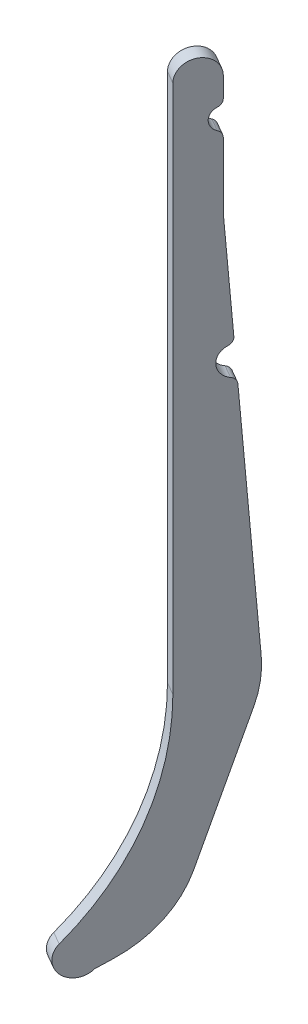
SolidWorks part; units mm, degrees
ref_plane "Front Plane" through (0, 0, 0) normal (0, 0, 1) x (1, 0, 0)
ref_plane "Top Plane" through (0, 0, 0) normal (0, 1, 0) x (1, 0, 0)
ref_plane "Right Plane" through (0, 0, 0) normal (1, 0, 0) x (0, 0, -1)
sketch "Sketch1" plane through (-22.6848, 0, -13.0971) normal (-0.866, 0, -0.5) x (-0.5, 0, 0.866)
  line L0 (-50.2251, -207.1163) -> (-50.2251, -63.6685) construction
  line L1 (-51.2251, -207.1163) -> (-51.2251, -63.6685)
  line L2 (25.7749, -207.1163) -> (-28.6723, -261.5635) construction
  line L3 (25.7749, -207.1163) -> (20.9854, -66.8615) construction
  line L4 (-61.2251, -96.0502) -> (-61.2251, -78.251)
  line L5 (-61.2251, -96.0502) -> (-63.3181, -125.3186)
  line L6 (-67.3143, -212.7397) -> (-55.3285, -249.1114)
  line L7 (-39.2993, -267.0104) -> (-35.7434, -268.6346)
  line L8 (-61.2251, -69.0859) -> (-61.2251, -63.6685)
  line L9 (-61.2251, -207.1163) -> (-61.2251, -63.6685) construction
  line L10 (-64.1251, -136.6035) -> (-68.7451, -201.2104)
  circle A0 centre (25.7749, -207.1163) radius 76 construction
  arc A1 (-50.2251, -207.1163) -> (25.7749, -283.1163) centre (25.7749, -207.1163) ccw construction
  arc A2 (-51.2251, -207.1163) -> (-28.6723, -261.5635) centre (25.7749, -207.1163) ccw
  arc A3 (-55.3285, -249.1114) -> (-39.2993, -267.0104) centre (-26.8357, -239.722) ccw
  arc A4 (-51.2251, -207.1163) -> (25.7749, -284.1163) centre (25.7749, -207.1163) ccw construction
  arc A5 (-28.6723, -261.5635) -> (-35.7434, -268.6346) centre (-32.2078, -265.099) cw
  arc A6 (-51.2251, -63.6685) -> (-61.2251, -63.6685) centre (-56.2251, -63.6685) ccw
  arc A7 (-61.2251, -207.1163) -> (-35.7434, -268.6346) centre (25.7749, -207.1163) ccw construction
  arc A8 (-68.7451, -201.2104) -> (-67.3143, -212.7397) centre (-38.8215, -203.3503) ccw
  arc A9 (-60.0251, -76.418) -> (-60.0251, -70.9189) centre (-61.2251, -73.6685) ccw
  arc A10 (-60.0251, -70.9189) -> (-61.2251, -69.0859) centre (-59.2251, -69.0859) cw
  arc A11 (-60.0251, -76.418) -> (-61.2251, -78.251) centre (-59.2251, -78.251) ccw
  arc A12 (-62.6606, -134.8178) -> (-62.1226, -127.2945) centre (-63.7216, -130.961) ccw
  arc A13 (-62.6606, -134.8178) -> (-64.1251, -136.6035) centre (-62.1302, -136.7461) ccw
  arc A14 (-62.1226, -127.2945) -> (-63.3181, -125.3186) centre (-61.3232, -125.4613) cw
  point P31 (-61.2251, -70.6685)
  point P39 (-64.0069, -134.9509)
  dimension "D1" = 1
  dimension "D3" = 30
  dimension "D4" = 35
  dimension "D5" = 2
  dimension "D6" = 4
  dimension "D7" = 2
  dimension "D2" = 10
extrude "Boss-Extrude1" add sketch "Sketch1" along normal blind 4 contours L1 A6 L8 A10 A9 A11 L4 L5 A14 A12 A13 L10 A8 L6 A3 L7 A5 A2
